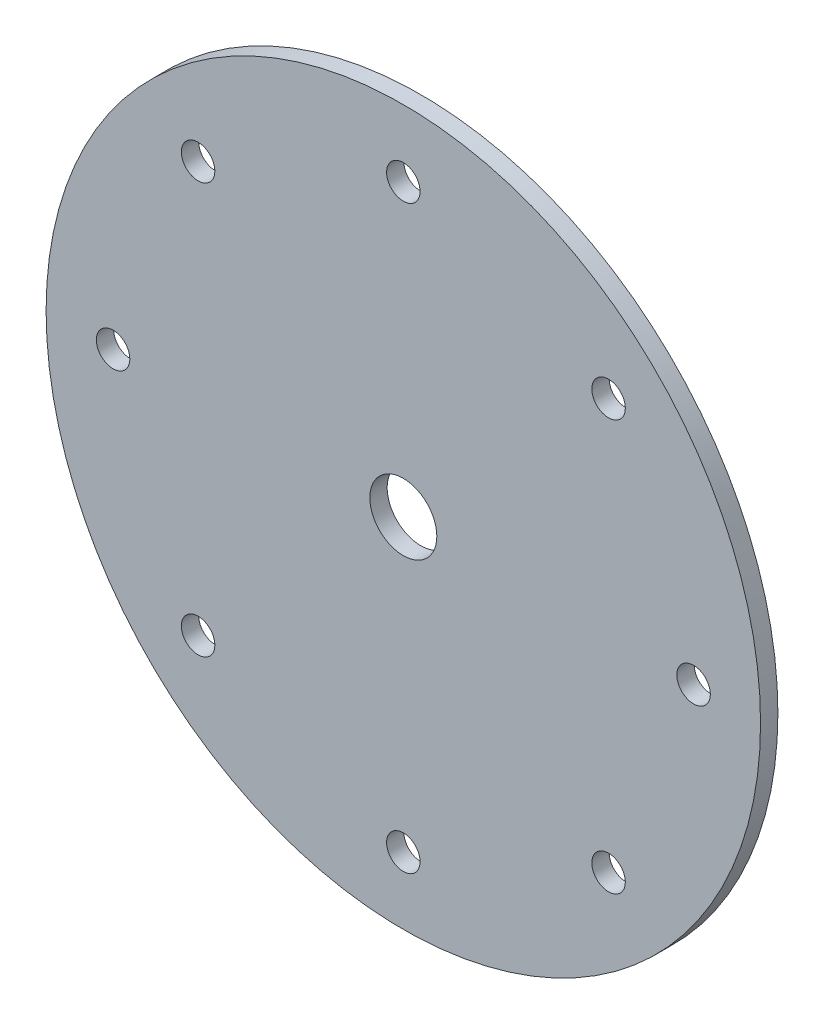
SolidWorks part; units mm, degrees
material "Plain Carbon Steel"
ref_plane "Front Plane" through (0, 0, 0) normal (0, 0, 1) x (1, 0, 0)
ref_plane "Top Plane" through (0, 0, 0) normal (0, 1, 0) x (1, 0, 0)
ref_plane "Right Plane" through (0, 0, 0) normal (1, 0, 0) x (0, 0, -1)
sketch "Sketch1" plane through (0, 0, 0) normal (0, 0, 1) x (1, 0, 0)
  line L0 (0, 101.6) -> (0, -101.6) construction
  line L1 (-101.6, 0) -> (101.6, 0) construction
  line L2 (-58.3717, 58.3717) -> (58.3717, -58.3717) construction
  line L3 (-58.3717, -58.3717) -> (58.3717, 58.3717) construction
  circle A0 centre (0, 0) radius 101.6
  circle A1 centre (0, 0) radius 9.525
  circle A2 centre (0, 82.55) radius 4.7625
  circle A6 centre (58.3717, 58.3717) radius 4.7625
  circle A7 centre (82.55, 0) radius 4.7625
  circle A8 centre (58.3717, -58.3717) radius 4.7625
  circle A9 centre (0, -82.55) radius 4.7625
  circle A10 centre (-58.3717, -58.3717) radius 4.7625
  circle A11 centre (-82.55, 0) radius 4.7625
  circle A12 centre (-58.3717, 58.3717) radius 4.7625
  dimension "D1" = 203.2
  dimension "D2" = 19.05
  dimension "D3" = 9.525
  dimension "D6" = 19.05
  dimension "D4" = 19.05
  dimension "D5" = 8
extrude "Rotor Disc" add sketch "Sketch1" along normal blind 4.9352
